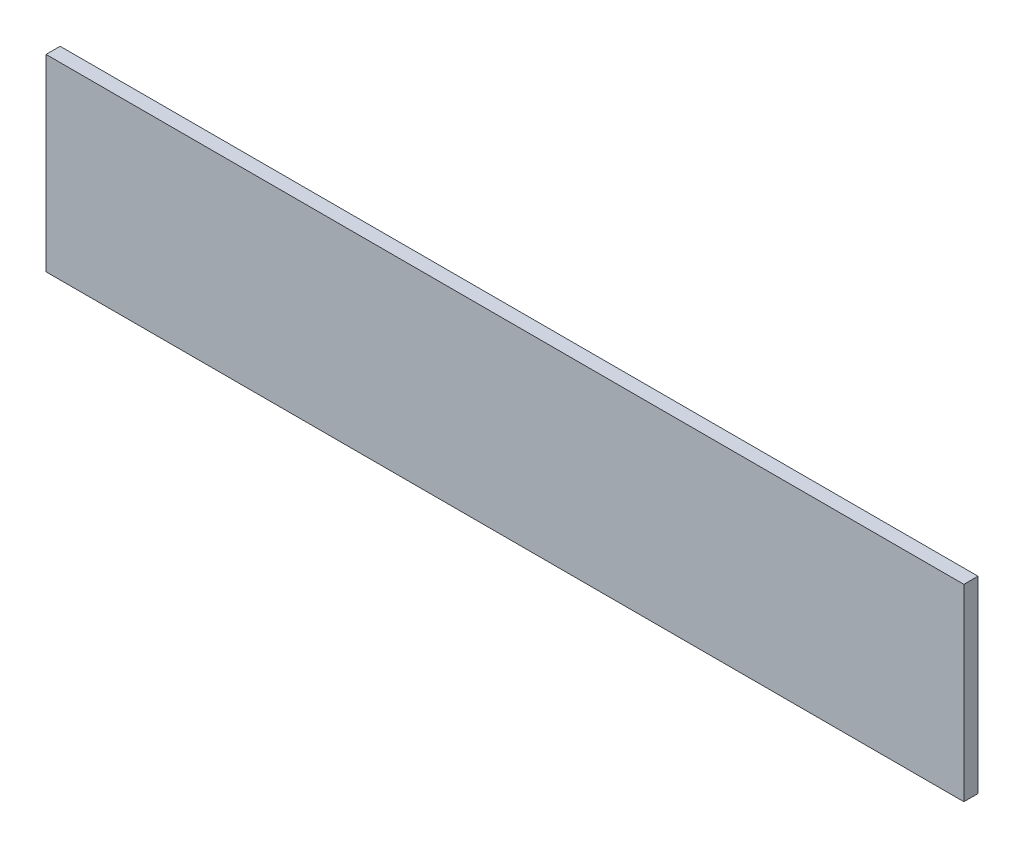
SolidWorks part; units mm, degrees
ref_plane "Plan de face" through (0, 0, 0) normal (0, 0, 1) x (1, 0, 0)
ref_plane "Plan de dessus" through (0, 0, 0) normal (0, 1, 0) x (1, 0, 0)
ref_plane "Plan de droite" through (0, 0, 0) normal (1, 0, 0) x (0, 0, -1)
sketch "Esquisse1" plane through (0, 0, 0) normal (0, 0, 1) x (1, 0, 0)
  line L1 (-134.1398, 32.1106) -> (60.8602, 32.1106)
  line L2 (-134.1398, 32.1106) -> (-134.1398, -7.8894)
  line L3 (-134.1398, -7.8894) -> (60.8602, -7.8894)
  line L4 (60.8602, 32.1106) -> (60.8602, -7.8894)
extrude "Boss.-Extru.1" add sketch "Esquisse1" along normal blind 3
